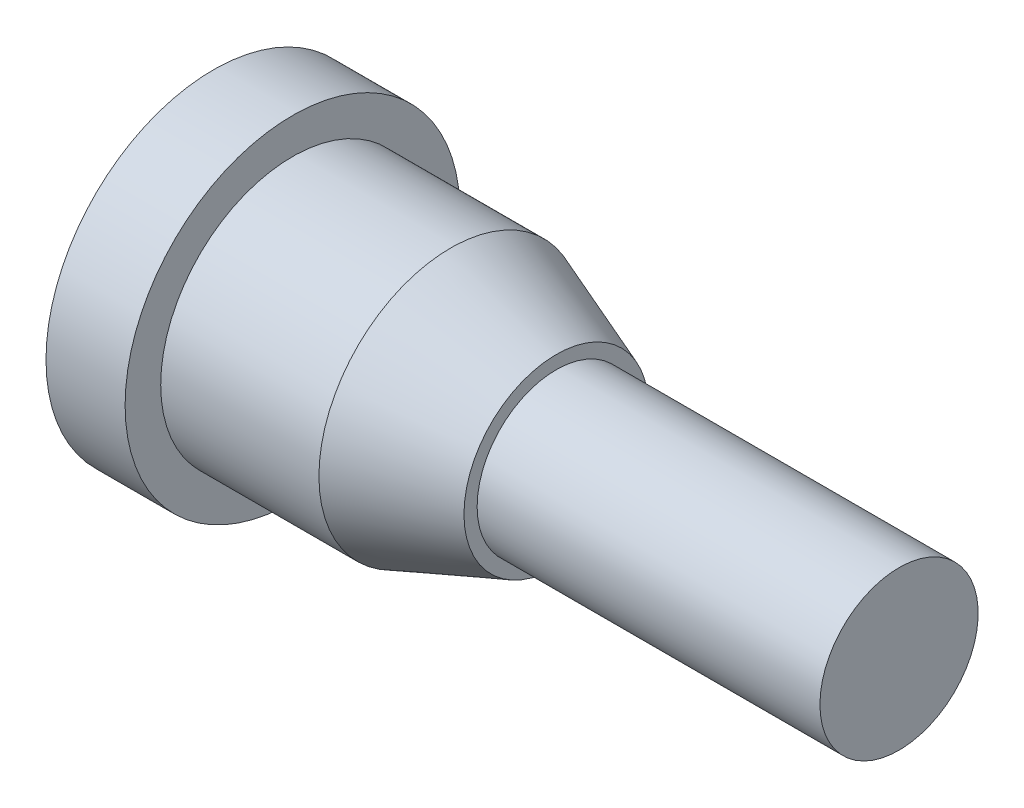
SolidWorks part; units mm, degrees
material "Alloy Steel (SS)"
ref_plane "Front Plane" through (0, 0, 0) normal (0, 0, 1) x (1, 0, 0)
ref_plane "Top Plane" through (0, 0, 0) normal (0, 1, 0) x (1, 0, 0)
ref_plane "Right Plane" through (0, 0, 0) normal (1, 0, 0) x (0, 0, -1)
sketch "Sketch1" plane through (0, 0, 0) normal (0, 0, 1) x (1, 0, 0)
  line L0 (0, 0) -> (0, 6.35)
  line L1 (0, 6.35) -> (3, 6.35)
  line L2 (3, 6.35) -> (3, 5)
  line L3 (3, 5) -> (9, 5)
  line L4 (9, 5) -> (13, 3.5)
  line L5 (13, 3.5) -> (13, 3)
  line L6 (26, 3) -> (26, 0)
  line L7 (26, 0) -> (0, 0)
  line L8 (13, 3) -> (26, 3)
  line L9 (-5.0325, 0) -> (26.1868, 0) construction
  dimension "D1" = 6.35
  dimension "D2" = 5
  dimension "D3" = 10
  dimension "D4" = 3
  dimension "D5" = 0.5
  dimension "D6" = 6
  dimension "D7" = 3
  dimension "D8" = 13
revolve "Revolve1" add sketch "Sketch1" angle 360 about L9
